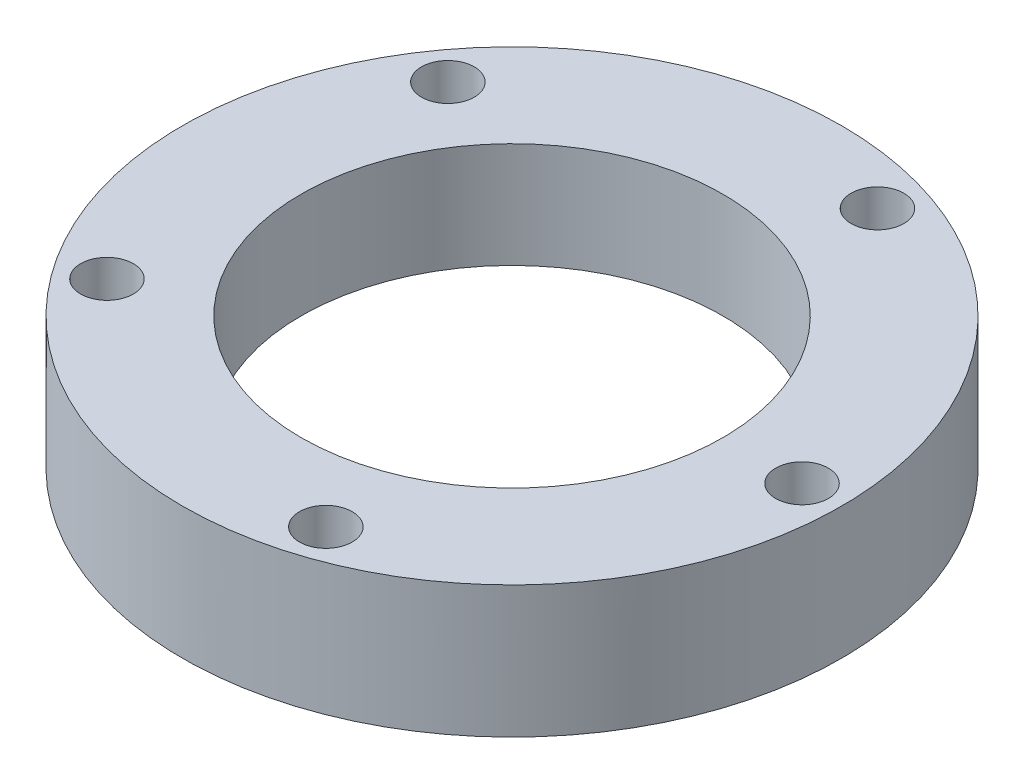
SolidWorks part; units mm, degrees
ref_plane "前视基准面" through (0, 0, 0) normal (0, 0, 1) x (1, 0, 0)
ref_plane "上视基准面" through (0, 0, 0) normal (0, 1, 0) x (1, 0, 0)
ref_plane "右视基准面" through (0, 0, 0) normal (1, 0, 0) x (0, 0, -1)
sketch "草图1" plane through (0, 0, 0) normal (0, 1, 0) x (1, 0, 0)
  circle A0 centre (0, 0) radius 12.5
extrude "凸台-拉伸1" add sketch "草图1" along normal blind 4
sketch "草图2" plane through (0, 4, 0) normal (0, 1, 0) x (1, 0, 0)
  circle A0 centre (0, 0) radius 10 construction
  circle A1 centre (10, 0) radius 1
  circle A2 centre (3.3992, -10.4616) radius 1
  circle A3 centre (-8.5902, -7.4167) radius 1
  circle A4 centre (-9.3992, 4.9268) radius 1
  circle A5 centre (2.0902, 9.5106) radius 1
  point P15 (-0.5, -0.6882)
  dimension "D1" = 5
extrude "凸台-拉伸2" add sketch "草图2" along normal blind 7.5
sketch "草图4" plane through (0, 4, 0) normal (0, 1, 0) x (1, 0, 0)
  circle A0 centre (0, 0) radius 12.5
sketch "草图5" plane through (0, 4, 0) normal (0, 1, 0) x (1, 0, 0)
  circle A0 centre (0, 0) radius 6
extrude "切除-拉伸1" cut sketch "草图5" against normal blind 10
sketch "草图7" plane through (0, 11.5, 0) normal (0, 1, 0) x (1, 0, 0)
  circle A0 centre (-8.5902, -7.4167) radius 1 construction
  circle A1 centre (-9.3992, 4.9268) radius 1 construction
  circle A2 centre (2.0902, 9.5106) radius 1 construction
  circle A3 centre (10, 0) radius 1 construction
  circle A4 centre (3.3992, -10.4616) radius 1 construction
  circle A5 centre (-8.5902, -7.4167) radius 1
  circle A6 centre (-9.3992, 4.9268) radius 1
  circle A7 centre (2.0902, 9.5106) radius 1
  circle A8 centre (10, 0) radius 1
  circle A9 centre (3.3992, -10.4616) radius 1
extrude "切除-拉伸2" cut sketch "草图7" against normal up to surface (7.5 mm away) contours A6 up to face at (0, 4, 6)
sketch "草图8" plane through (0, 4, 0) normal (0, 1, 0) x (1, 0, 0)
  circle A0 centre (0, 0) radius 6 construction
  circle A1 centre (0, 0) radius 12.5
  circle A2 centre (0, 0) radius 12.5
  circle A3 centre (0, 0) radius 6
  dimension "D1" = 0
extrude "切除-拉伸3" cut sketch "草图8" along normal blind 10
sketch "草图9" plane through (0, 4, 0) normal (0, 1, 0) x (1, 0, 0)
  circle A0 centre (11, 0) radius 1
  circle A1 centre (3.3992, -10.4616) radius 1
  circle A2 centre (-8.8992, -6.4656) radius 1
  circle A3 centre (-8.8992, 6.4656) radius 1
  circle A4 centre (3.3992, 10.4616) radius 1
  point P14 (0, 0)
  dimension "D1" = 5
extrude "凸台-拉伸3" add sketch "草图9" along normal blind 10
sketch "草图10" plane through (0, 14, 0) normal (0, 1, 0) x (1, 0, 0)
  circle A0 centre (3.3992, -10.4616) radius 1 construction
  circle A1 centre (-8.8992, -6.4656) radius 1
  circle A2 centre (-8.8992, -6.4656) radius 1
  circle A3 centre (11, 0) radius 1 construction
  circle A4 centre (3.3992, 10.4616) radius 1 construction
  circle A5 centre (-8.8992, 6.4656) radius 1 construction
  circle A6 centre (3.3992, -10.4616) radius 1
  circle A7 centre (11, 0) radius 1
  circle A8 centre (3.3992, 10.4616) radius 1
  circle A9 centre (-8.8992, 6.4656) radius 1
  dimension "D1" = 0
extrude "切除-拉伸4" cut sketch "草图10" against normal blind 14
sketch "草图11" plane through (0, 4, 0) normal (0, 1, 0) x (1, 0, 0)
  circle A0 centre (0, 0) radius 8
extrude "切除-拉伸5" cut sketch "草图11" against normal blind 10
sketch "草图12" plane through (0, 4, 0) normal (0, 1, 0) x (1, 0, 0)
  circle A0 centre (0, 0) radius 12.5
  circle A1 centre (0, 0) radius 9.6
sketch "草图13" plane through (0, 0, 0) normal (0, -1, 0) x (1, 0, 0)
  circle A0 centre (0, 0) radius 9.6
  circle A1 centre (0, 0) radius 12.5
  circle A2 centre (0, 0) radius 12.5
  dimension "D1" = 0
extrude "凸台-拉伸5" add sketch "草图13" along normal blind 1
